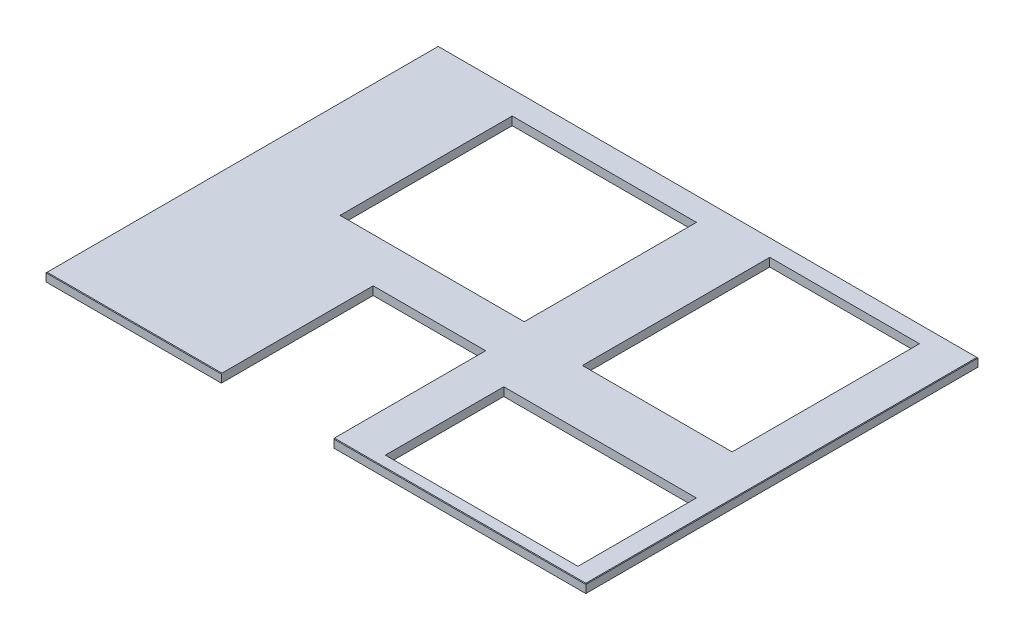
SolidWorks part; units mm, degrees
material "Oak"
ref_plane "Front Plane" through (0, 0, 0) normal (0, 0, 1) x (1, 0, 0)
ref_plane "Top Plane" through (0, 0, 0) normal (0, 1, 0) x (1, 0, 0)
ref_plane "Right Plane" through (0, 0, 0) normal (1, 0, 0) x (0, 0, -1)
sketch "Sketch1" plane through (0, 0, 0) normal (0, 1, 0) x (1, 0, 0)
  line L4 (2438.4, 0) -> (2438.4, 1771.65)
  line L5 (2438.4, 1771.65) -> (0, 1771.65)
  line L7 (0, 0) -> (2438.4, 0)
  line L8 (0, 1771.65) -> (0, 0)
  dimension "D1" = 2438.4
  dimension "D5" = 1771.65
extrude "Boss-Extrude1" add sketch "Sketch1" against normal blind 38.1
chamfer "Chamfer1" distance 2.54 angle 45 4 edges at (1219.2, 0, -1771.65) (2438.4, 0, -885.825) (1219.2, 0, 0) (0, 0, -885.825)
sketch "Sketch2" plane through (0, 0, 0) normal (0, 1, 0) x (1, 0, 0)
  line L0 (2.54, 1769.11) -> (2.54, 2.54) construction
  line L1 (1482.09, 585.7875) -> (2352.04, 585.7875)
  line L2 (1482.09, 585.7875) -> (1482.09, 50.8)
  line L3 (1482.09, 50.8) -> (2352.04, 50.8)
  line L4 (2352.04, 585.7875) -> (2352.04, 50.8)
  dimension "D1" = 869.95
  dimension "D2" = 534.9875
  dimension "D3" = 1479.55
  dimension "D4" = 50.8
extrude "Cut-Extrude1" cut sketch "Sketch2" against normal through all
sketch "Sketch3" plane through (0, 0, 0) normal (0, 1, 0) x (1, 0, 0)
  line L1 (792.1625, 685.8) -> (1300.1625, 685.8)
  line L2 (792.1625, 685.8) -> (792.1625, 0)
  line L3 (792.1625, 0) -> (1300.1625, 0)
  line L4 (1300.1625, 685.8) -> (1300.1625, 0)
  line L5 (2438.4, 0) -> (0, 0) construction
  dimension "D1" = 508
  dimension "D2" = 792.1625
  dimension "D3" = 685.8
extrude "Cut-Extrude2" cut sketch "Sketch3" against normal through all
sketch "Sketch4" plane through (0, 0, 0) normal (0, 1, 0) x (1, 0, 0)
  line L1 (1576.4256, 1692.91) -> (2252.6269, 1692.91)
  line L2 (1576.4256, 1692.91) -> (1576.4256, 846.5769)
  line L3 (1576.4256, 846.5769) -> (2252.6269, 846.5769)
  line L4 (2252.6269, 1692.91) -> (2252.6269, 846.5769)
  dimension "D1" = 1576.4256
  dimension "D2" = 676.2013
  dimension "D3" = 1692.91
  dimension "D4" = 846.3331
extrude "Cut-Extrude3" cut sketch "Sketch4" against normal through all
sketch "Sketch5" plane through (0, 0, 0) normal (0, 1, 0) x (1, 0, 0)
  line L1 (441.7996, 1664.0628) -> (1273.9707, 1664.0628)
  line L2 (441.7996, 1664.0628) -> (441.7996, 886.3577)
  line L3 (441.7996, 886.3577) -> (1273.9707, 886.3577)
  line L4 (1273.9707, 1664.0628) -> (1273.9707, 886.3577)
extrude "Cut-Extrude4" cut sketch "Sketch5" against normal through all
